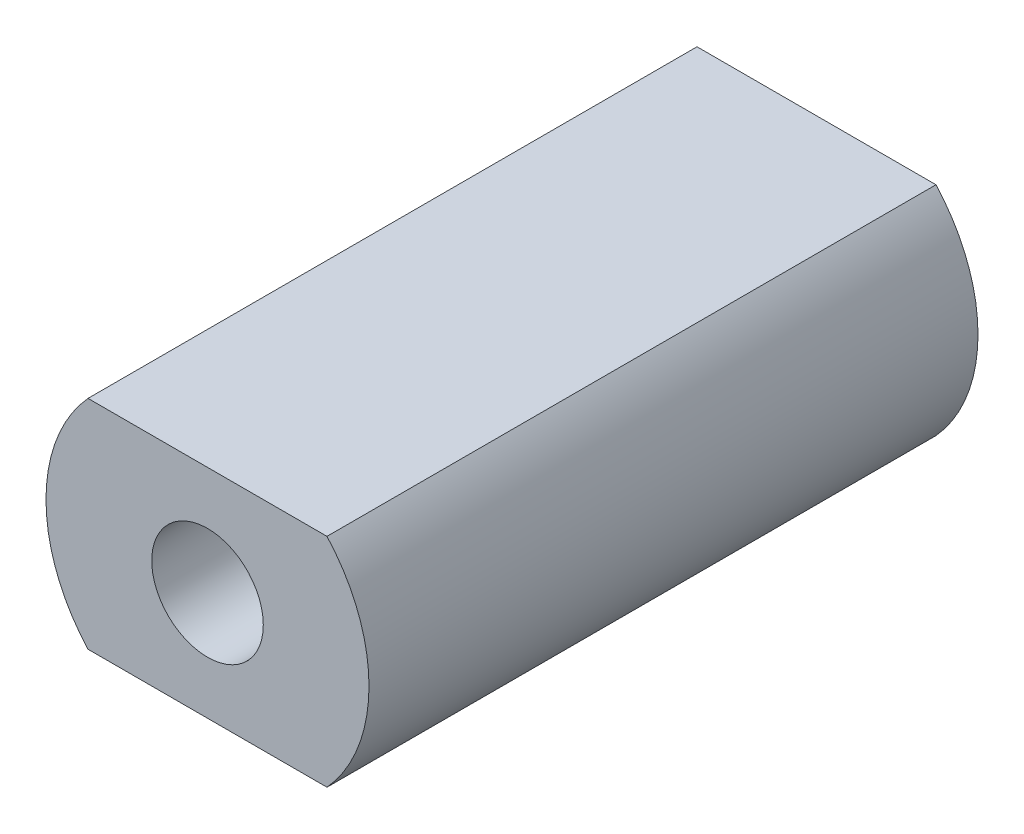
SolidWorks part; units mm, degrees
ref_plane "Front Plane" through (0, 0, 0) normal (0, 0, 1) x (1, 0, 0)
ref_plane "Top Plane" through (0, 0, 0) normal (0, 1, 0) x (1, 0, 0)
ref_plane "Right Plane" through (0, 0, 0) normal (1, 0, 0) x (0, 0, -1)
sketch "Sketch1" plane through (0, 0, 0) normal (0, 0, 1) x (1, 0, 0)
  line L0 (-2.0347, 0) -> (2.0347, 0) construction
  line L1 (-2.0347, 1.85) -> (2.0347, 1.85)
  line L2 (-2.0347, 1.85) -> (-2.0347, -1.85) construction
  line L3 (-2.0347, -1.85) -> (2.0347, -1.85)
  line L4 (2.0347, 1.85) -> (2.0347, -1.85) construction
  arc A0 (-2.0347, 1.85) -> (-2.0347, -1.85) centre (0, 0) ccw
  circle A1 centre (0, 0) radius 0.95
  arc A2 (2.0347, -1.85) -> (2.0347, 1.85) centre (0, 0) ccw
  dimension "D2" = 5.5
  dimension "D3" = 1.9
  dimension "D1" = 3.7
extrude "Boss-Extrude1" add sketch "Sketch1" along normal blind 10.37
